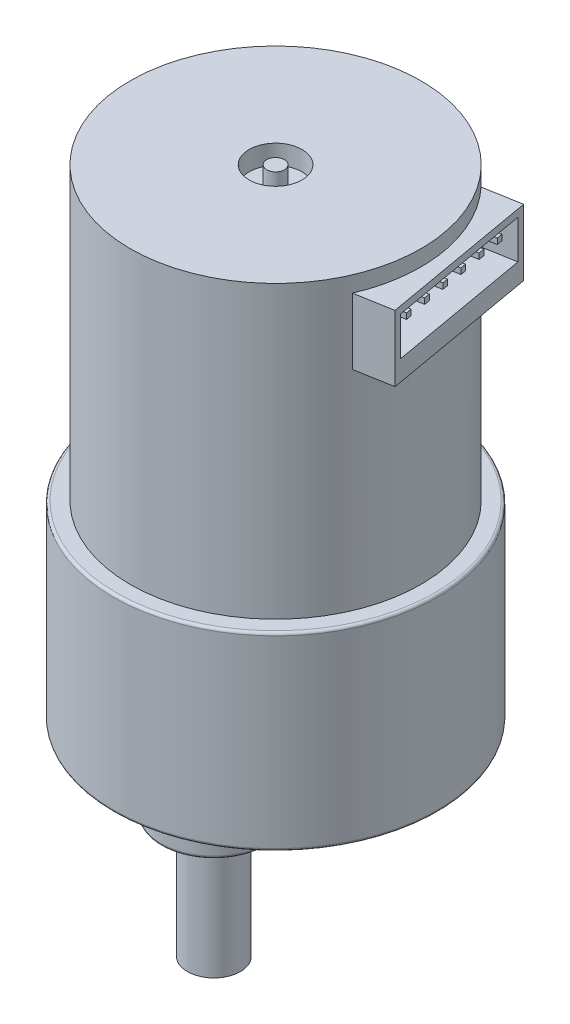
SolidWorks part; units mm, degrees
ref_plane "Front" through (0, 0, 0) normal (0, 0, 1) x (1, 0, 0)
ref_plane "Top" through (0, 0, 0) normal (0, 1, 0) x (1, 0, 0)
ref_plane "Right" through (0, 0, 0) normal (1, 0, 0) x (0, 0, -1)
sketch "草图1" plane through (0, 0, 0) normal (0, 1, 0) x (1, 0, 0)
  circle A0 centre (0, 0) radius 18.4
  dimension "D1" = 36.8
extrude "凸台-拉伸1" add sketch "草图1" along normal blind 21.5
sketch "草图2" plane through (0, 0, 0) normal (0, -1, 0) x (1, 0, 0)
  line L0 (-31.6805, 0) -> (24.9484, 0) construction
  line L1 (0, 27.2007) -> (0, -26.1116) construction
  circle A0 centre (0, 7) radius 6
  dimension "D1" = 12
  dimension "D2" = 7
extrude "凸台-拉伸2" add sketch "草图2" along normal blind 6
sketch "草图3" plane through (0, -6, 0) normal (0, -1, 0) x (1, 0, 0)
  circle A0 centre (0, 7) radius 3
  dimension "D1" = 6
extrude "凸台-拉伸3" add sketch "草图3" along normal blind 13.8
sketch "草图4" plane through (0, -19.8, 0) normal (0, -1, 0) x (1, 0, 0)
  line L0 (-4.5376, 4.5) -> (4.4344, 4.5)
  line L1 (4.4344, 4.5) -> (4.4344, 1.9562)
  line L2 (4.4344, 1.9562) -> (-4.5376, 1.9562)
  line L3 (-4.5376, 1.9562) -> (-4.5376, 4.5)
  line L4 (0, 10) -> (0, 4) construction
  circle A0 centre (0, 7) radius 3 construction
  circle A1 centre (0, 7) radius 3 construction
  dimension "D1" = 5.5
extrude "切除-拉伸1" cut sketch "草图4" against normal blind 12
sketch "草图6" plane through (0, 0, 0) normal (0, -1, 0) x (1, 0, 0)
  line L0 (-18.4, 0) -> (18.4, 0) construction
  circle A0 centre (0, 0) radius 18.4 construction
  circle A1 centre (-15.5, 0) radius 1.5
  circle A2 centre (-7.75, 13.4234) radius 1.5
  circle A3 centre (7.75, 13.4234) radius 1.5
  circle A4 centre (15.5, 0) radius 1.5
  circle A5 centre (7.75, -13.4234) radius 1.5
  circle A6 centre (-7.75, -13.4234) radius 1.5
  point P21 (0, 0)
  dimension "D1" = 3
  dimension "D2" = 15.5
  dimension "D3" = 6
extrude "切除-拉伸2" cut sketch "草图6" against normal blind 6
sketch "草图7" plane through (0, 0, 0) normal (0, -1, 0) x (1, 0, 0)
  arc A0 (-9.9866, 7.5179) -> (9.9866, 7.5179) centre (0, 0) ccw
  arc A1 (-9.9866, 7.5179) -> (9.9866, 7.5179) centre (0, 7) ccw
  circle A2 centre (0, 7) radius 6 construction
  dimension "D1" = 25
  dimension "D2" = 4
extrude "切除-拉伸3" cut sketch "草图7" against normal blind 0.72
sketch "草图8" plane through (0, 21.5, 0) normal (0, 1, 0) x (1, 0, 0)
  circle A0 centre (0, 0) radius 16.5
  dimension "D1" = 33
extrude "凸台-拉伸4" add sketch "草图8" along normal blind 33
sketch "草图9" plane through (0, 0, 0) normal (1, 0, 0) x (0, 0, -1)
  line L0 (0, 58.2642) -> (0, -11.6265) construction
ref_plane "基准面1" through (0, 0, 0) normal (-0.9848, 0, 0.1736) x (0, -1, 0)
sketch "草图10" plane through (0, 0, 0) normal (-0.9848, 0, 0.1736) x (0, -1, 0)
  line L0 (-54.5, 16.5) -> (-54.5, -16.5) construction
  line L1 (-45.2, 9) -> (-52.7, 9)
  line L2 (-45.2, 9) -> (-45.2, -9)
  line L3 (-45.2, -9) -> (-52.7, -9)
  line L4 (-52.7, 9) -> (-52.7, -9)
  line L5 (-58.2642, 0) -> (11.6265, 0) construction
  dimension "D1" = 1.8
  dimension "D2" = 7.5
  dimension "D3" = 18
  dimension "D4" = 9
extrude "凸台-拉伸5" add sketch "草图10" against normal blind 18
sketch "草图11" plane through (17.7265, 0, -3.1257) normal (0.9848, 0, -0.1736) x (-0.1736, 0, -0.9848)
  line L0 (9, 52.7) -> (-9, 52.7) construction
  line L1 (-8.2, 51.9) -> (8.2, 51.9)
  line L2 (-8.2, 51.9) -> (-8.2, 46)
  line L3 (-8.2, 46) -> (8.2, 46)
  line L4 (8.2, 51.9) -> (8.2, 46)
  line L5 (9, 52.7) -> (9, 45.2) construction
  line L6 (9, 45.2) -> (-9, 45.2) construction
  line L7 (-9, 45.2) -> (-9, 52.7) construction
  dimension "D1" = 0.8
  dimension "D2" = 0.8
  dimension "D3" = 0.8
  dimension "D4" = 0.8
extrude "切除-拉伸4" cut sketch "草图11" against normal blind 5
sketch "草图12" plane through (12.8025, 0, -2.2574) normal (0.9848, 0, -0.1736) x (-0.1736, 0, -0.9848)
  line L0 (8.2, 51.9) -> (-8.2, 51.9) construction
  line L1 (-1.59, 50.26) -> (-0.95, 50.26)
  line L2 (-1.59, 50.26) -> (-1.59, 50.9)
  line L3 (-1.59, 50.9) -> (-0.95, 50.9)
  line L4 (-0.95, 50.26) -> (-0.95, 50.9)
  line L5 (-1.59, 50.26) -> (-0.95, 50.9) construction
  line L6 (-1.59, 50.9) -> (-0.95, 50.26) construction
  line L7 (0, 58.2642) -> (0, -11.6265) construction
  line L8 (0.95, 50.26) -> (0.95, 50.9)
  line L9 (0.95, 50.26) -> (1.59, 50.26)
  line L10 (1.59, 50.26) -> (1.59, 50.9)
  line L11 (0.95, 50.9) -> (1.59, 50.9)
  line L12 (3.49, 50.26) -> (3.49, 50.9)
  line L13 (3.49, 50.26) -> (4.13, 50.26)
  line L14 (4.13, 50.26) -> (4.13, 50.9)
  line L15 (3.49, 50.9) -> (4.13, 50.9)
  line L16 (6.03, 50.26) -> (6.03, 50.9)
  line L17 (6.03, 50.26) -> (6.67, 50.26)
  line L18 (6.67, 50.26) -> (6.67, 50.9)
  line L19 (6.03, 50.9) -> (6.67, 50.9)
  line L20 (-8.2, 46) -> (8.2, 46) construction
  line L21 (0, 51.9) -> (0, 46) construction
  line L22 (8.2, 51.9) -> (-8.2, 51.9) construction
  line L23 (-6.03, 50.26) -> (-6.67, 50.26)
  line L24 (-6.67, 50.26) -> (-6.67, 50.9)
  line L25 (-6.03, 50.9) -> (-6.67, 50.9)
  line L26 (-6.03, 50.26) -> (-6.03, 50.9)
  line L27 (-3.49, 50.26) -> (-4.13, 50.26)
  line L28 (-4.13, 50.26) -> (-4.13, 50.9)
  line L29 (-3.49, 50.9) -> (-4.13, 50.9)
  line L30 (-3.49, 50.26) -> (-3.49, 50.9)
  point P0 (-1.27, 50.58)
  dimension "D1" = 1
  dimension "D2" = 0.64
  dimension "D3" = 1.27
  dimension "D4" = 4
extrude "凸台-拉伸6" add sketch "草图12" along normal offset from surface (4.5 mm away) 0.5 up to face at (17.7265, 48.95, -3.1257)
sketch "草图13" plane through (12.8025, 0, -2.2574) normal (0.9848, 0, -0.1736) x (-0.1736, 0, -0.9848)
  line L0 (8.2, 46) -> (8.2, 51.9) construction
  line L1 (-8.2, 46) -> (8.2, 46)
  line L2 (-8.2, 46) -> (-8.2, 47.5)
  line L3 (-8.2, 47.5) -> (8.2, 47.5)
  line L4 (8.2, 46) -> (8.2, 47.5)
  dimension "D1" = 1.5
extrude "凸台-拉伸7" add sketch "草图13" along normal up to surface (5 mm away) up to face at (17.7265, 48.95, -3.1257)
sketch "草图14" plane through (0, 54.5, 0) normal (0, 1, 0) x (1, 0, 0)
  circle A0 centre (0, 0) radius 3
  dimension "D1" = 6
extrude "切除-拉伸5" cut sketch "草图14" against normal blind 2.2
sketch "草图15" plane through (0, 52.3, 0) normal (0, 1, 0) x (1, 0, 0)
  circle A0 centre (0, 0) radius 1
  dimension "D1" = 2
extrude "凸台-拉伸8" add sketch "草图15" along normal up to surface (2.2 mm away) up to face at (0, 54.5, 3)
chamfer "倒角1" distance 0.7 angle 45 2 edges at (0, 0, -12.5) (0, 0, -3)
fillet "圆角1" radius 0.3 1 edges at (0, -6, 1)
fillet "圆角2" radius 0.3 2 edges at (0, 0, 18.4) (0, 21.5, 18.4)
